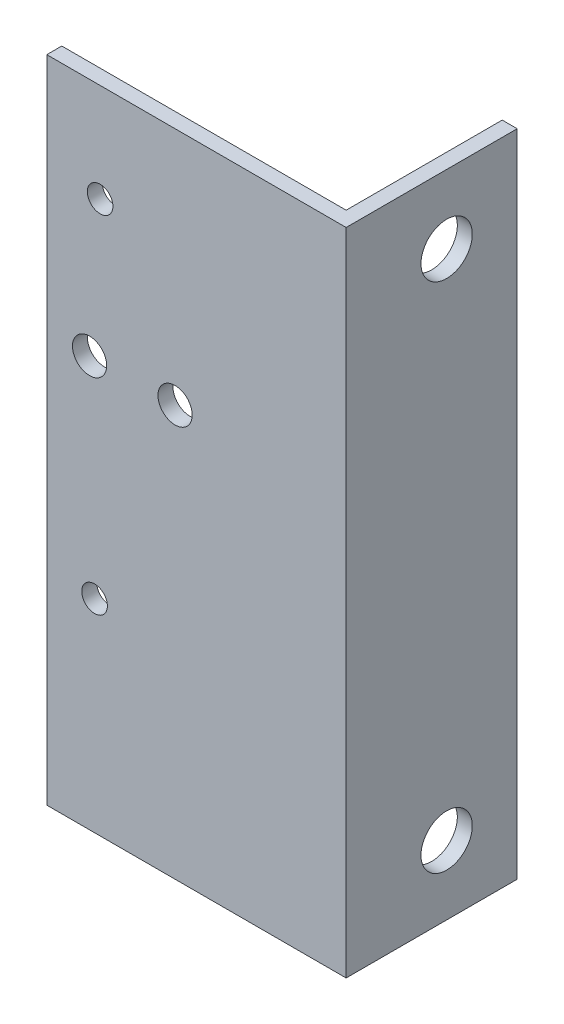
SolidWorks part; units mm, degrees
ref_plane "Front Plane" through (0, 0, 0) normal (0, 0, 1) x (1, 0, 0)
ref_plane "Top Plane" through (0, 0, 0) normal (0, 1, 0) x (1, 0, 0)
ref_plane "Right Plane" through (0, 0, 0) normal (1, 0, 0) x (0, 0, -1)
sketch "Sketch1" plane through (0, 0, 0) normal (0, 1, 0) x (1, 0, 0)
  line L0 (-35, 0) -> (-35, -1.75)
  line L1 (0, -1.75) -> (-35, -1.75)
  line L2 (0, -1.75) -> (0, 18.25)
  line L3 (0, 18.25) -> (-35, 18.25) construction
  line L4 (-35, -1.75) -> (-35, 18.25) construction
  line L5 (0, -1.75) -> (-35, 18.25) construction
  line L6 (0, 18.25) -> (-35, -1.75) construction
  line L7 (-35, 18.25) -> (-1.75, 18.25) construction
  line L8 (-35, 18.25) -> (-35, 0) construction
  line L9 (-35, 0) -> (-1.75, 0)
  line L10 (-1.75, 18.25) -> (-1.75, 0)
  line L11 (-18.375, 0) -> (-18.375, 18.25) construction
  line L12 (-35, 9.125) -> (-1.75, 9.125) construction
  line L13 (-1.75, 18.25) -> (0, 18.25)
  line L15 (0, -55) -> (0, 55) construction
  line L18 (-55, 0) -> (55, 0) construction
  point P0 (-17.5, 8.25)
  point P113 (-18.375, 9.125)
  dimension "D1" = 35
  dimension "D2" = 20
  dimension "D3" = 1.75
  dimension "D4" = 1.75
extrude "Boss-Extrude1" add sketch "Sketch1" along normal blind 76
sketch "Sketch3" plane through (-1.75, 0, 0) normal (-1, 0, 0) x (0, 0, 1)
  line L0 (-18.25, 76) -> (0, 76) construction
  line L1 (-18.25, 76) -> (-18.25, 0) construction
  line L2 (-18.25, 0) -> (0, 0) construction
  line L4 (0, 76) -> (0, 0) construction
  line L5 (0, 76) -> (-20, 76) construction
  line L6 (0, 76) -> (0, 22.4241) construction
  line L7 (0, 22.4241) -> (-20, 22.4241) construction
  line L8 (-20, 76) -> (-20, 22.4241) construction
  line L9 (-10, 22.4241) -> (-10, 76) construction
  line L10 (0, 49.2121) -> (-20, 49.2121) construction
  circle A0 centre (-10, 8.05) radius 3
  circle A1 centre (-10, 19.5) radius 2.25 construction
  circle A2 centre (-10, 56.5) radius 3 construction
  circle A3 centre (-10, 67.955) radius 3
  point P154 (-10, 49.2121)
  dimension "D1" = 6
  dimension "D2" = 4.5
  dimension "D3" = 6
  dimension "D4" = 6
  dimension "D5" = 8.045
  dimension "D6" = 19.5
  dimension "D7" = 8.05
  dimension "D8" = 19.5
  dimension "D9" = 8.25
  dimension "D10" = 20
extrude "Cut-Extrude1" cut sketch "Sketch3" against normal up to next
sketch "Sketch4" plane through (0, 0, 1.75) normal (0, 0, 1) x (1, 0, 0)
  line L0 (-35, 76) -> (-35, 0) construction
  line L1 (-35, 76) -> (-35, 0) construction
  line L2 (-35, 76) -> (0, 76) construction
  circle A0 centre (-28.767, 64.5) radius 1.5
  circle A1 centre (-29.417, 23.7) radius 1.5
  circle A2 centre (-30, 48) radius 2
  circle A3 centre (-20, 48) radius 2
  dimension "D1" = 3
  dimension "D4" = 3
  dimension "D6" = 4
  dimension "D7" = 4
  dimension "D2" = 6.233
  dimension "D3" = 11.5
  dimension "D5" = 52.3
  dimension "D8" = 10
  dimension "D9" = 28
  dimension "D10" = 5
  dimension "D11" = 5.583
extrude "Cut-Extrude2" cut sketch "Sketch4" against normal up to next
sketch "Sketch5" plane through (0, 0, 1.75) normal (0, 0, 1) x (1, 0, 0)
  line L0 (-35, 76) -> (-35, 0) construction
  line L1 (-35, 0) -> (0, 0) construction
  line L3 (-35, 76) -> (-35, 0) construction
  circle A0 centre (-27.017, 11.5) radius 2.9732
  circle A1 centre (-29.4, 52.3) radius 1.5
  circle A2 centre (-30, 28) radius 2
  circle A3 centre (-20, 28) radius 2
  dimension "D1" = 5.9465
  dimension "D4" = 3
  dimension "D6" = 4
  dimension "D7" = 4
  dimension "D2" = 5.6
  dimension "D3" = 11.5
  dimension "D5" = 40.8
  dimension "D8" = 10
  dimension "D9" = 5
  dimension "D10" = 28
  dimension "D11" = 7.983
extrude "Cut-Extrude3" [suppressed] cut sketch "Sketch5" against normal up to next
equation "\"larg\"=35"
equation "\"D1@Sketch1\"=\"larg\""
equation "\"alt\"=20"
equation "\"D2@Sketch1\"=\"alt\""
equation "\"thik\"=1.75"
equation "\"D3@Sketch1\"=\"thik\""
equation "\"D4@Sketch1\"=\"thik\""
